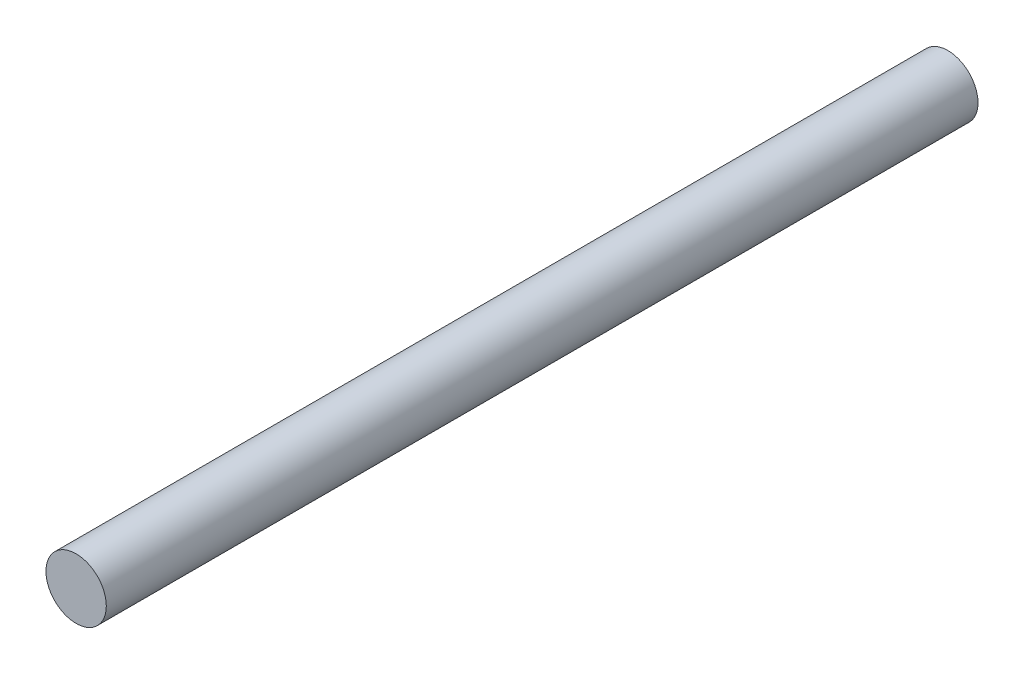
SolidWorks part; units mm, degrees
ref_plane "Front Plane" through (0, 0, 0) normal (0, 0, 1) x (1, 0, 0)
ref_plane "Top Plane" through (0, 0, 0) normal (0, 1, 0) x (1, 0, 0)
ref_plane "Right Plane" through (0, 0, 0) normal (1, 0, 0) x (0, 0, -1)
sketch "Sketch1" plane through (0, 0, 0) normal (0, 0, 1) x (1, 0, 0)
  circle A0 centre (0, 0) radius 1.143
  dimension "D1" = 2.286
extrude "Boss-Extrude1" add sketch "Sketch1" along normal blind 33.02
